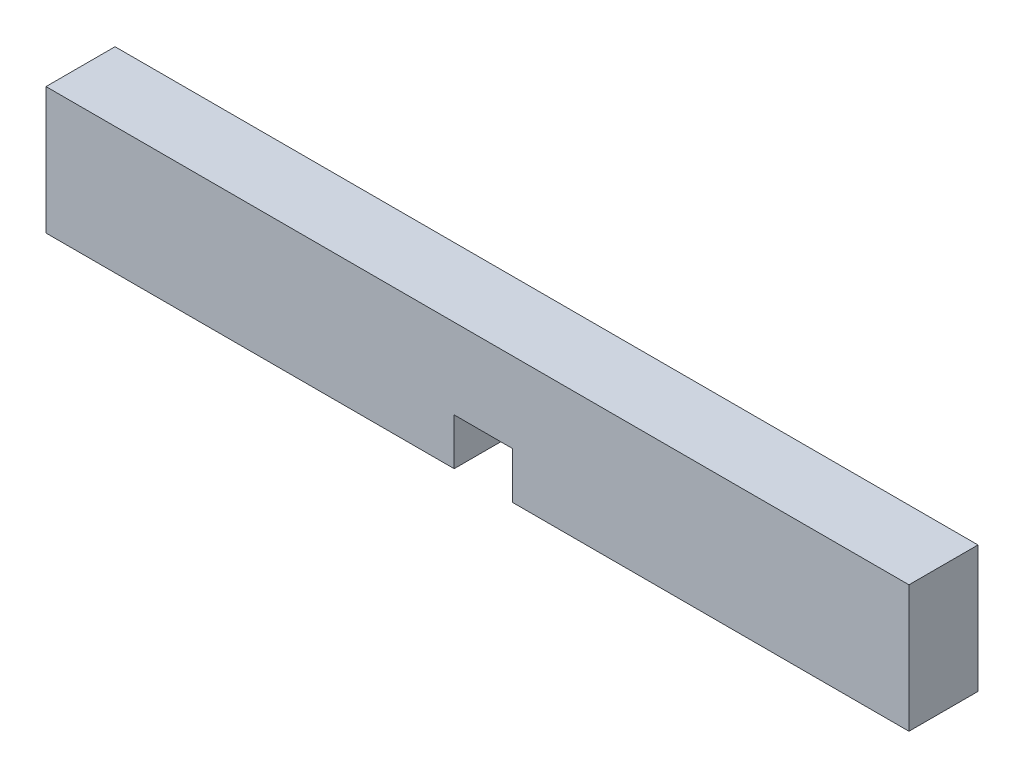
SolidWorks part; units mm, degrees
ref_plane "Front Plane" through (0, 0, 0) normal (0, 0, 1) x (1, 0, 0)
ref_plane "Top Plane" through (0, 0, 0) normal (0, 1, 0) x (1, 0, 0)
ref_plane "Right Plane" through (0, 0, 0) normal (1, 0, 0) x (0, 0, -1)
sketch "Sketch1" plane through (0, 0, 0) normal (0, 0, 1) x (1, 0, 0)
  line L1 (0, 0) -> (58.7375, 0)
  line L2 (0, 0) -> (0, 8.636)
  line L3 (0, 8.636) -> (58.7375, 8.636)
  line L4 (58.7375, 0) -> (58.7375, 8.636)
  dimension "D1" = 58.7375
  dimension "D2" = 8.636
extrude "Extrude1" add sketch "Sketch1" along normal blind 4.699
sketch "Sketch3" plane through (0, 0, 4.699) normal (0, 0, 1) x (1, 0, 0)
  line L0 (0, 0) -> (58.7375, 0) construction
  line L1 (27.7812, 0) -> (31.75, 0)
  line L2 (27.7812, 0) -> (27.7812, 3.175)
  line L3 (27.7812, 3.175) -> (31.75, 3.175)
  line L4 (31.75, 0) -> (31.75, 3.175)
  line L5 (0, 8.636) -> (0, 0) construction
  dimension "D1" = 3.9688
  dimension "D2" = 27.7812
  dimension "D3" = 3.175
extrude "Cut-Extrude1" cut sketch "Sketch3" against normal through all
